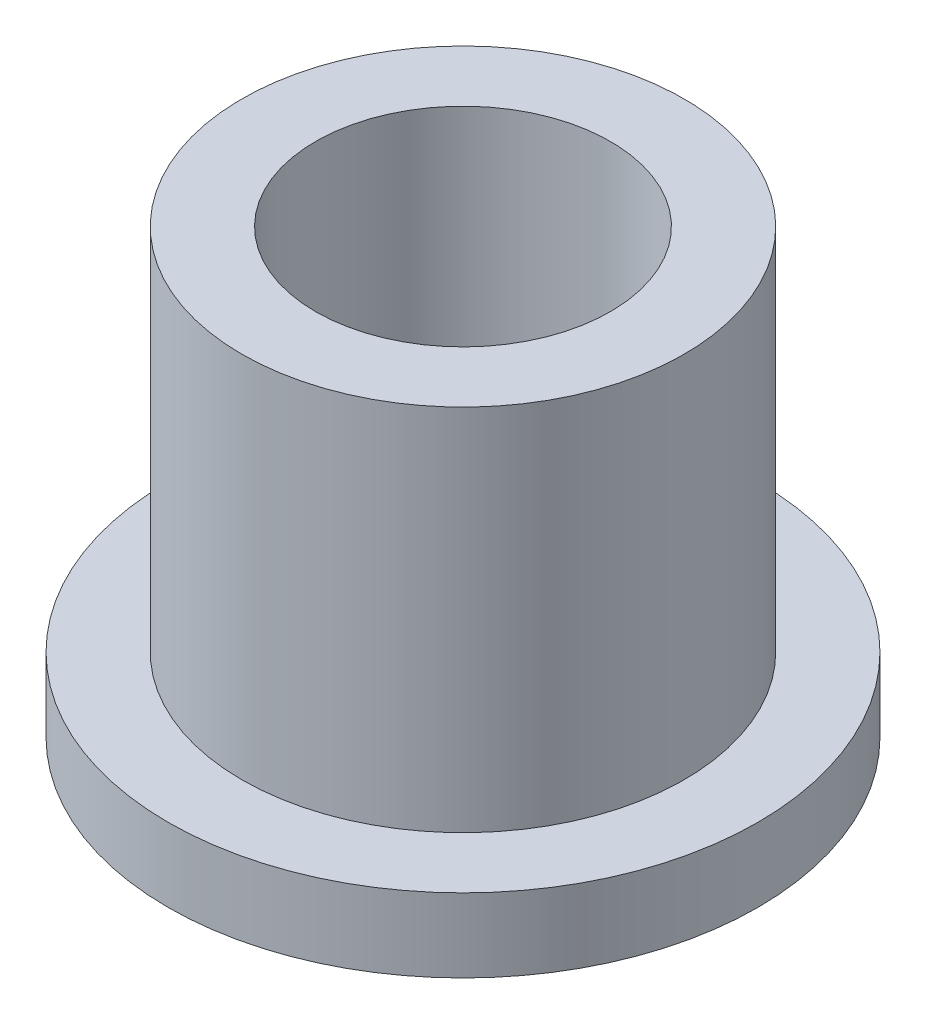
SolidWorks part; units mm, degrees
ref_plane "Front" through (0, 0, 0) normal (0, 0, 1) x (1, 0, 0)
ref_plane "Top" through (0, 0, 0) normal (0, 1, 0) x (1, 0, 0)
ref_plane "Right" through (0, 0, 0) normal (1, 0, 0) x (0, 0, -1)
sketch "Sketch1" plane through (0, 0, 0) normal (0, 1, 0) x (1, 0, 0)
  circle A0 centre (0, 0) radius 3.175
  circle A1 centre (0, 0) radius 4.7625
  circle A2 centre (0, 0) radius 6.35
  dimension "ID" = 6.35
  dimension "OD" = 9.525
  dimension "FlangeOD" = 12.7
sketch "Sketch2" plane through (0, 0, 0) normal (0, 1, 0) x (1, 0, 0)
  circle A0 centre (0, 0) radius 3.175 construction
  circle A1 centre (0, 0) radius 4.7625 construction
  circle A2 centre (0, 0) radius 3.175
  circle A3 centre (0, 0) radius 4.7625
extrude "Boss-Extrude1" add sketch "Sketch2" along normal blind 9.525
sketch "Sketch3" plane through (0, 0, 0) normal (0, 1, 0) x (1, 0, 0)
  circle A0 centre (0, 0) radius 6.35 construction
  circle A1 centre (0, 0) radius 4.7625 construction
  circle A2 centre (0, 0) radius 6.35
  circle A3 centre (0, 0) radius 4.7625
extrude "Boss-Extrude2" add sketch "Sketch3" along normal blind 1.5875
